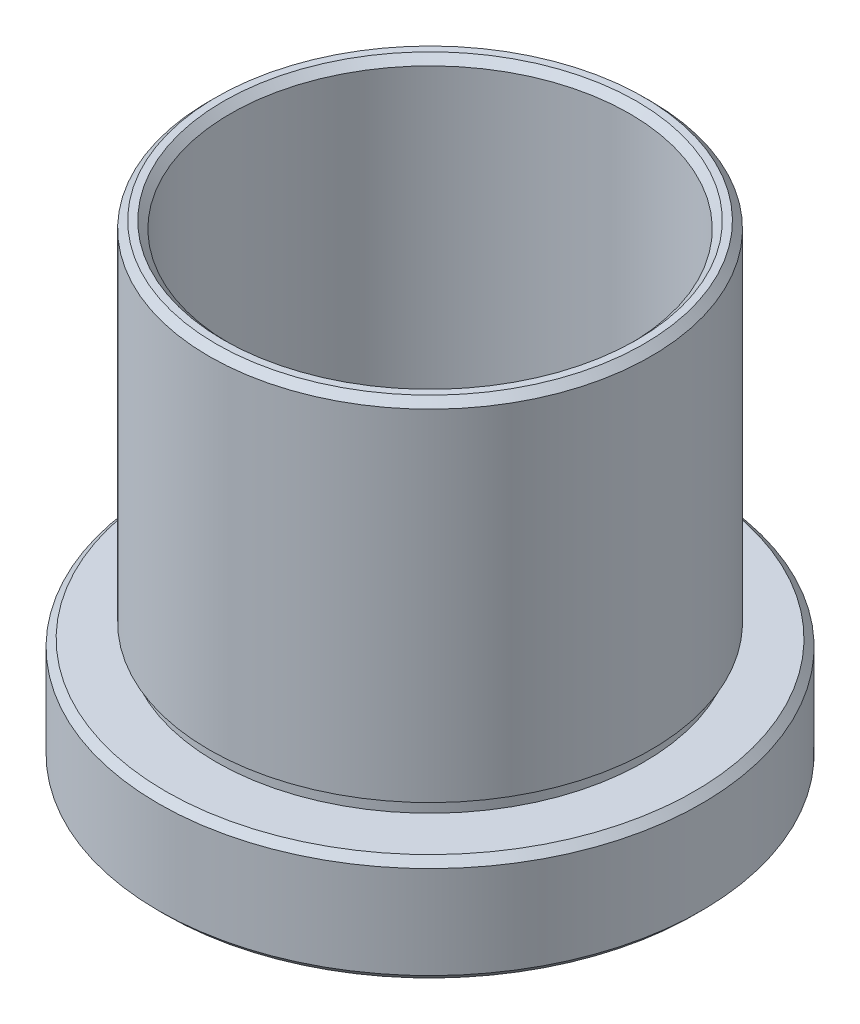
SolidWorks part; units mm, degrees
ref_plane "前视基准面" through (0, 0, 0) normal (0, 0, 1) x (1, 0, 0)
ref_plane "上视基准面" through (0, 0, 0) normal (0, 1, 0) x (1, 0, 0)
ref_plane "右视基准面" through (0, 0, 0) normal (1, 0, 0) x (0, 0, -1)
sketch "草图1" plane through (0, 0, 0) normal (0, 0, 1) x (1, 0, 0)
  line L0 (0, 44.5986) -> (0, -38.4055) construction
  line L1 (14.5, 27.0429) -> (15, 27.0429)
  line L2 (15.5, 26.5429) -> (15.5, 2.6429)
  line L3 (15.5, 2.6429) -> (15, 2.6429)
  line L4 (15, 2.6429) -> (15, 1.6429)
  line L5 (15, 1.6429) -> (18.55, 1.6429)
  line L6 (19.05, 1.1429) -> (19.05, -5.3571)
  line L7 (18.55, -5.8571) -> (18, -5.8571)
  line L8 (17.5, -5.3571) -> (17.5, -1.3571)
  line L9 (17.5, -1.3571) -> (17.6, -1.3571)
  line L10 (17.6, -1.3571) -> (17.6, -0.3571)
  line L11 (19.05, -5.3571) -> (18.55, -5.8571)
  line L12 (14, -0.3571) -> (14, 26.5429)
  line L13 (17.6, -0.3571) -> (14, -0.3571)
  line L14 (18, -5.8571) -> (17.5, -5.3571)
  line L15 (15, 27.0429) -> (15.5, 26.5429)
  line L16 (14, 26.5429) -> (14.5, 27.0429)
  line L17 (18.55, 1.6429) -> (19.05, 1.1429)
  point P3 (14, 27.0429)
  point P4 (15.5, 27.0429)
  point P9 (19.05, -5.8571)
  point P10 (19.05, 1.6429)
  point P11 (17.5, -5.8571)
  point P13 (15, 2.1429)
  point P14 (17.6, -0.8571)
  dimension "D2" = 19.05
  dimension "D3" = 17.5
  dimension "D4" = 15.5
  dimension "D5" = 14
  dimension "D6" = 7.5
  dimension "D7" = 5.5
  dimension "D8" = 1
  dimension "D9" = 1
  dimension "D10" = 15
  dimension "D11" = 17.6
revolve "旋转2" add sketch "草图1" angle 360 about L0
